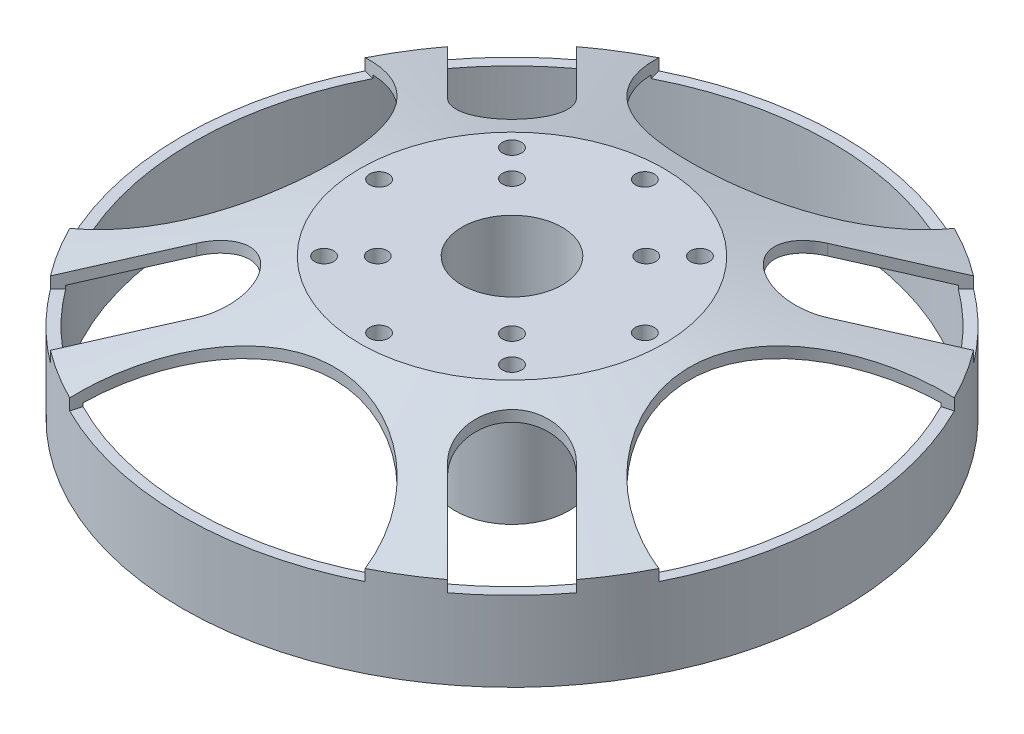
SolidWorks part; units mm, degrees
ref_plane "Front Plane" through (0, 0, 0) normal (0, 0, 1) x (1, 0, 0)
ref_plane "Top Plane" through (0, 0, 0) normal (0, 1, 0) x (1, 0, 0)
ref_plane "Right Plane" through (0, 0, 0) normal (1, 0, 0) x (0, 0, -1)
sketch "Sketch1" plane through (0, 0, 0) normal (0, 1, 0) x (1, 0, 0)
  circle A0 centre (0, 0) radius 43.4
  circle A1 centre (0, 0) radius 42
  dimension "D1" = 86.8
  dimension "D2" = 1.4
extrude "Boss-Extrude1" add sketch "Sketch1" along normal blind 10.5
sketch "Sketch2" plane through (0, 0, 0) normal (0, 0, 1) x (1, 0, 0)
  line L0 (0, 18.5) -> (-20, 18.5)
  line L1 (-43.4, 10.5) -> (-43.4, 12)
  line L2 (-43.4, 0) -> (43.4, 0) construction
  line L3 (0, 18.5) -> (0, 16.2)
  line L4 (0, 16.2) -> (-23.0492, 16.2)
  line L5 (-42, 10.5) -> (-42, 10.9359)
  line L6 (-43.4, 10.5) -> (-42, 10.5)
  line L8 (-43.4, 12) -> (-20, 18.5)
  line L9 (-42, 10.9359) -> (-23.0492, 16.2)
  dimension "D1" = 20
  dimension "D2" = 18.5
  dimension "D3" = 2.3
  dimension "D4" = 1.5
  dimension "D5" = 1.4
revolve "Revolve1" add sketch "Sketch2" angle 360 about L3
sketch "Sketch3" plane through (0, 16.2, 0) normal (0, -1, 0) x (1, 0, 0)
  circle A0 centre (0, 0) radius 8.5
  dimension "D1" = 17
extrude "Boss-Extrude2" add sketch "Sketch3" along normal blind 5
sketch "Sketch4" plane through (0, 11.2, 0) normal (0, -1, 0) x (1, 0, 0)
  circle A0 centre (0, 0) radius 7.5
  dimension "D1" = 15
extrude "Boss-Extrude3" add sketch "Sketch4" along normal blind 18
sketch "Sketch5" plane through (0, 18.5, 0) normal (0, 1, 0) x (1, 0, 0)
  circle A0 centre (0, 0) radius 6.6
  dimension "D1" = 13.2
extrude "Cut-Extrude1" cut sketch "Sketch5" against normal blind 20
sketch "Sketch6" plane through (0, -6.8, 0) normal (0, -1, 0) x (1, 0, 0)
  circle A0 centre (0, 0) radius 3
  dimension "D1" = 6
extrude "Cut-Extrude2" cut sketch "Sketch6" against normal through all
sketch "Sketch7" plane through (0, 18.5, 0) normal (0, 1, 0) x (1, 0, 0)
  line L0 (-30.6884, 30.6884) -> (-20.7889, 20.7889) construction
  line L1 (-26.4458, 34.9311) -> (-16.5463, 25.0316)
  line L2 (-34.9311, 26.4458) -> (-25.0316, 16.5463)
  line L3 (-20.7889, 20.7889) -> (0, 0) construction
  line L4 (0, 43.4) -> (0, 0) construction
  line L5 (26.4458, 34.9311) -> (16.5463, 25.0316)
  line L6 (34.9311, 26.4458) -> (25.0316, 16.5463)
  line L7 (30.6884, 30.6884) -> (20.7889, 20.7889) construction
  line L8 (34.9311, -26.4458) -> (25.0316, -16.5463)
  line L9 (26.4458, -34.9311) -> (16.5463, -25.0316)
  line L10 (30.6884, -30.6884) -> (20.7889, -20.7889) construction
  line L11 (-26.4458, -34.9311) -> (-16.5463, -25.0316)
  line L12 (-34.9311, -26.4458) -> (-25.0316, -16.5463)
  line L13 (-30.6884, -30.6884) -> (-20.7889, -20.7889) construction
  circle A0 centre (0, 43.4) radius 20
  circle A1 centre (0, 0) radius 43.4 construction
  circle A2 centre (43.4, 0) radius 20
  circle A3 centre (0, -43.4) radius 20
  circle A4 centre (-43.4, 0) radius 20
  arc A5 (-26.4458, 34.9311) -> (-34.9311, 26.4458) centre (-30.6884, 30.6884) ccw
  arc A6 (-25.0316, 16.5463) -> (-16.5463, 25.0316) centre (-20.7889, 20.7889) ccw
  arc A7 (34.9311, 26.4458) -> (26.4458, 34.9311) centre (30.6884, 30.6884) ccw
  arc A8 (16.5463, 25.0316) -> (25.0316, 16.5463) centre (20.7889, 20.7889) ccw
  arc A9 (26.4458, -34.9311) -> (34.9311, -26.4458) centre (30.6884, -30.6884) ccw
  arc A10 (25.0316, -16.5463) -> (16.5463, -25.0316) centre (20.7889, -20.7889) ccw
  arc A11 (-34.9311, -26.4458) -> (-26.4458, -34.9311) centre (-30.6884, -30.6884) ccw
  arc A12 (-16.5463, -25.0316) -> (-25.0316, -16.5463) centre (-20.7889, -20.7889) ccw
  point P4 (-25.7387, 25.7387)
  point P14 (0, 0)
  point P25 (25.7387, 25.7387)
  point P32 (25.7387, -25.7387)
  point P39 (-25.7387, -25.7387)
  point P46 (0, 0)
  dimension "D1" = 40
  dimension "D4" = 6
  dimension "D3" = 45
  dimension "D5" = 14
  dimension "D2" = 4
  dimension "D6" = 4
extrude "Cut-Extrude3" cut sketch "Sketch7" against normal blind 8
sketch "Sketch8" plane through (0, 18.5, 0) normal (0, 1, 0) x (1, 0, 0)
  line L0 (0, 0) -> (16.5463, 16.5463) construction
  arc A0 (16.5463, 25.0316) -> (25.0316, 16.5463) centre (20.7889, 20.7889) ccw construction
  point P0 (12.3744, 12.3744)
  point P1 (8.8388, 8.8388)
  dimension "D1" = 12.5
  dimension "D2" = 17.5
hole_wizard "M3 Tapped Hole2" positions "3DSketch2" profile "Sketch11" tap size "M3" standard "ISO" end condition through all
sketch3d "3DSketch2"
  point P0 (12.3744, 18.5, -12.3744)
sketch "Sketch11" plane through (12.3744, 18.5, -12.3744) normal (1, 0, 0) x (0, 0, 1)
  line L0 (0, 0) -> (0, 25.3)
  line L1 (0, 25.3) -> (1.25, 25.3)
  line L2 (1.25, 25.3) -> (1.25, 0)
  line L5 (1.25, 0) -> (0, 0)
  line L11 (0, -6.35) -> (0, 107.95) construction
  dimension "Thru Tap Drill Dia." = 2.5
  dimension "Thru Tap Drill Depth" = 25.3
cosmetic thread "Hole Thread3" parameters "D2"=3
hole_wizard "M3 Tapped Hole3" positions "3DSketch3" profile "Sketch12" tap size "M3" standard "ISO" end condition through all
sketch3d "3DSketch3"
  point P0 (8.8388, 18.5, -8.8388)
sketch "Sketch12" plane through (8.8388, 18.5, -8.8388) normal (1, 0, 0) x (0, 0, 1)
  line L0 (0, 0) -> (0, 25.3)
  line L1 (0, 25.3) -> (1.25, 25.3)
  line L2 (1.25, 25.3) -> (1.25, 0)
  line L5 (1.25, 0) -> (0, 0)
  line L11 (0, -6.35) -> (0, 107.95) construction
  dimension "Thru Tap Drill Dia." = 2.5
  dimension "Thru Tap Drill Depth" = 25.3
cosmetic thread "Hole Thread4" parameters "D2"=3
pattern_circular "CirPattern1" count 8 over 360 about axis through (0, 0, 0) along (0, 1, 0) of "M3 Tapped Hole2"
cosmetic thread "Hole Thread5" parameters "D2"=3
cosmetic thread "Hole Thread6" parameters "D2"=3
cosmetic thread "Hole Thread7" parameters "D2"=3
cosmetic thread "Hole Thread8" parameters "D2"=3
cosmetic thread "Hole Thread9" parameters "D2"=3
cosmetic thread "Hole Thread10" parameters "D2"=3
cosmetic thread "Hole Thread11" parameters "D2"=3
pattern_circular "CirPattern2" count 4 over 360 about axis through (0, 0, 0) along (0, 1, 0) of "CirPattern1", "M3 Tapped Hole3"
cosmetic thread "Hole Thread12" parameters "D2"=3
cosmetic thread "Hole Thread13" parameters "D2"=3
cosmetic thread "Hole Thread14" parameters "D2"=3
